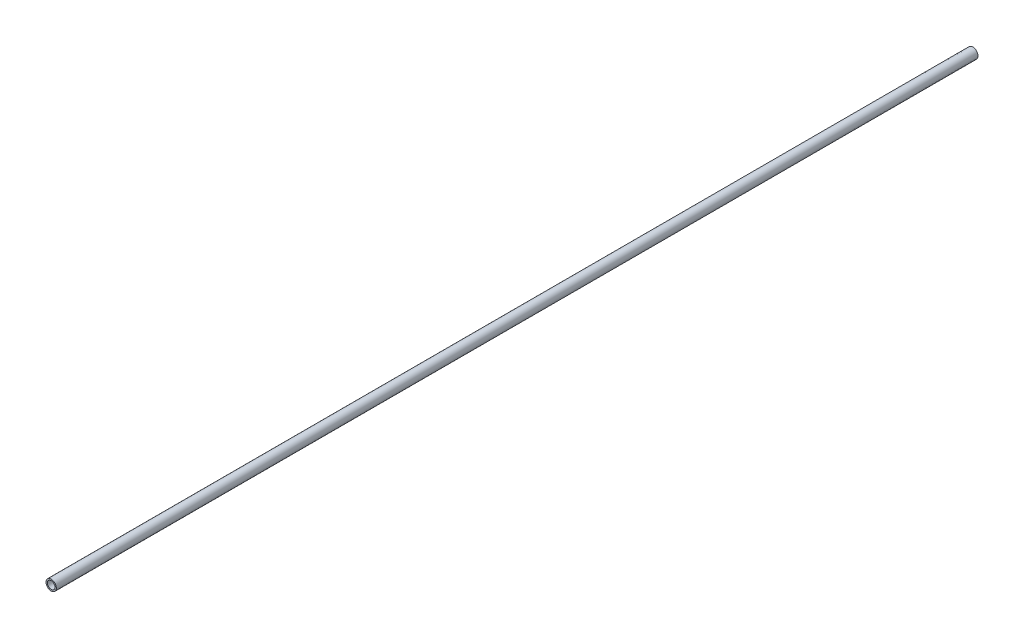
SolidWorks part; units mm, degrees
ref_plane "Front Plane" through (0, 0, 0) normal (0, 0, 1) x (1, 0, 0)
ref_plane "Top Plane" through (0, 0, 0) normal (0, 1, 0) x (1, 0, 0)
ref_plane "Right Plane" through (0, 0, 0) normal (1, 0, 0) x (0, 0, -1)
sketch "Sketch1" plane through (0, 0, 0) normal (0, 0, 1) x (1, 0, 0)
  circle A0 centre (0, 0) radius 8.5725
  dimension "Pipe OD" = 17.145
extrude "Extrude-Thin1" add sketch "Sketch1" along normal mid plane 1524 thin thin type one direction reverse wall 2.3114
